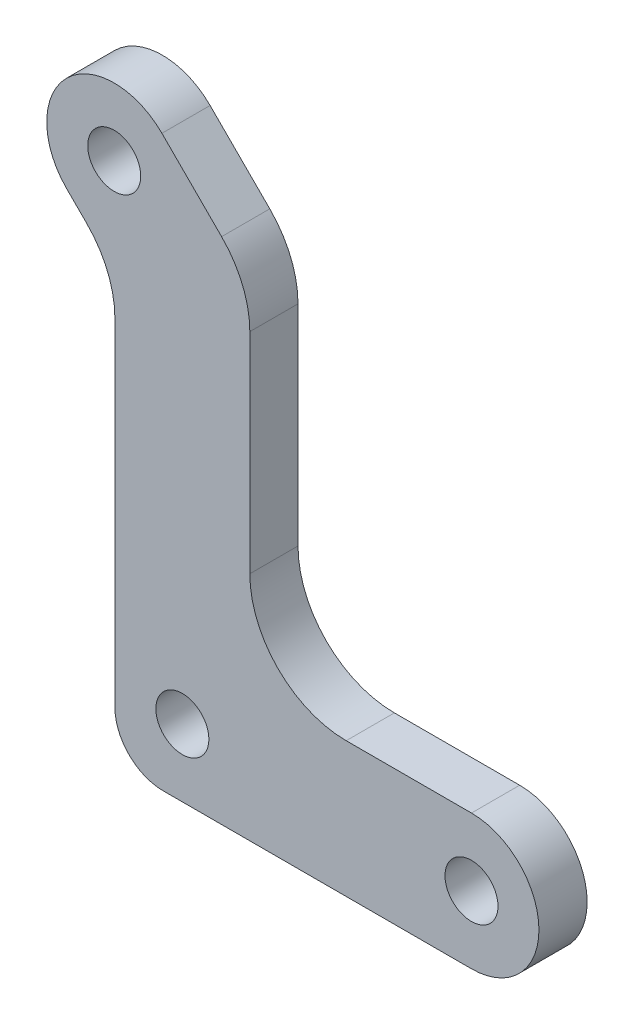
SolidWorks part; units mm, degrees
ref_plane "前基準面" through (0, 0, 0) normal (0, 0, 1) x (1, 0, 0)
ref_plane "上基準面" through (0, 0, 0) normal (0, 1, 0) x (1, 0, 0)
ref_plane "右基準面" through (0, 0, 0) normal (1, 0, 0) x (0, 0, -1)
sketch "草圖1" plane through (0, 0, 0) normal (0, 0, 1) x (1, 0, 0)
  line L0 (0, 40) -> (0, 0) construction
  line L1 (0, 0) -> (30, 0) construction
  line L2 (0, 40) -> (0, 48.7396) construction
  line L3 (0, 40) -> (-7.0711, 47.0711) construction
  line L4 (17, 7) -> (30, 7)
  line L5 (7, 38.7574) -> (7, 17)
  line L6 (4.0711, 45.8284) -> (-2.1213, 52.0208)
  line L7 (-2, -7) -> (30, -7)
  line L8 (-7, 32.9584) -> (-7, -2)
  line L9 (-9.9289, 40.0294) -> (-12.0208, 42.1213)
  line L10 (7, 42.8995) -> (7, 7) construction
  line L11 (7, 42.8995) -> (-2.1213, 52.0208) construction
  line L12 (-7, 37.1005) -> (-7, -7) construction
  line L13 (-7, 37.1005) -> (-12.0208, 42.1213) construction
  line L14 (-7, -7) -> (30, -7) construction
  line L15 (7, 7) -> (30, 7) construction
  circle A0 centre (0, 0) radius 2.75
  circle A1 centre (30, 0) radius 2.75
  circle A3 centre (-7.0711, 47.0711) radius 2.75
  arc A4 (30, 7) -> (30, -7) centre (30, 0) cw
  arc A5 (-2.1213, 52.0208) -> (-12.0208, 42.1213) centre (-7.0711, 47.0711) ccw
  arc A6 (7, 38.7574) -> (4.0711, 45.8284) centre (-3, 38.7574) ccw
  arc A7 (-7, 32.9584) -> (-9.9289, 40.0294) centre (-17, 32.9584) ccw
  arc A8 (-2, -7) -> (-7, -2) centre (-2, -2) cw
  arc A9 (17, 7) -> (7, 17) centre (17, 17) cw
  dimension "D1" = 5.5
  dimension "D2" = 5.5
  dimension "D4" = 7
  dimension "D6" = 10
  dimension "D8" = 10
  dimension "D9" = 5
  dimension "D10" = 10
  dimension "D3" = 30
  dimension "D5" = 45
  dimension "D7" = 7
extrude "填料-伸長1" add sketch "草圖1" along normal blind 5 contours A0 | L5 A9 L4 A4 L7 A8 L8 A7 L9 A5 L6 A6 | A3 | A1
